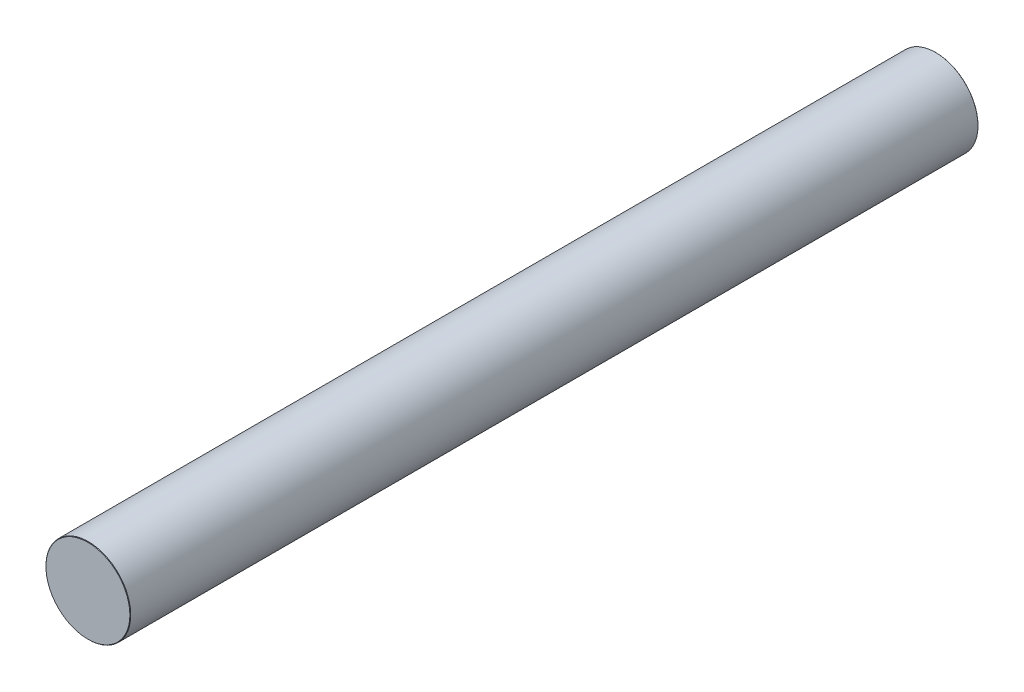
SolidWorks part; units mm, degrees
material "АД 31 ГОСТ 4784-97"
ref_plane "Plane1" through (0, 0, 0) normal (0, 0, 1) x (1, 0, 0)
ref_plane "Plane2" through (0, 0, 0) normal (0, 1, 0) x (1, 0, 0)
ref_plane "Plane3" through (0, 0, 0) normal (1, 0, 0) x (0, 0, -1)
sketch "Эскиз1" plane through (0, 0, 0) normal (0, 0, 1) x (1, 0, 0)
  circle A0 centre (0, 0) radius 10
  dimension "D1" = 20
extrude "Бобышка-Вытянуть1" add sketch "Эскиз1" along normal blind 200
chamfer "Фаска1" distance 0.1 angle 45 2 edges at (10, 0, 0) (10, 0, 200)
